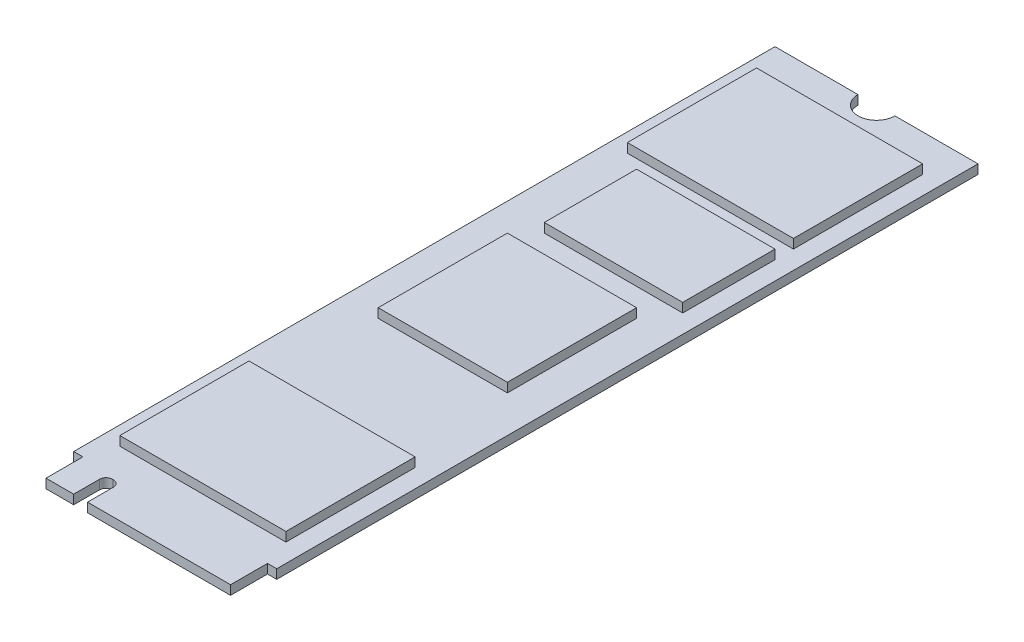
SolidWorks part; units mm, degrees
ref_plane "Front Plane" through (0, 0, 0) normal (0, 0, 1) x (1, 0, 0)
ref_plane "Top Plane" through (0, 0, 0) normal (0, 1, 0) x (1, 0, 0)
ref_plane "Right Plane" through (0, 0, 0) normal (1, 0, 0) x (0, 0, -1)
sketch "Sketch1" plane through (0, 0, 0) normal (0, 1, 0) x (1, 0, 0)
  line L0 (11, 40) -> (-11, 40)
  line L1 (11, 40) -> (11, -36)
  line L2 (11, -36) -> (10, -36)
  line L3 (10, -36) -> (10, -40)
  line L4 (10, -40) -> (-5.5, -40)
  line L5 (-5.5, -40) -> (-5.5, -37.2)
  line L6 (-6.2, -36.5) -> (-6.3, -36.5)
  line L7 (-7, -37.2) -> (-7, -40)
  line L8 (-7, -40) -> (-10, -40)
  line L9 (-10, -40) -> (-10, -36)
  line L10 (-10, -36) -> (-11, -36)
  line L11 (-11, -36) -> (-11, 40)
  arc A0 (-5.5, -37.2) -> (-6.2, -36.5) centre (-6.2, -37.2) ccw
  arc A1 (-6.3, -36.5) -> (-7, -37.2) centre (-6.3, -37.2) ccw
  point P14 (-5.5, -36.5)
  dimension "D13" = 0.7
  dimension "D1" = 22
  dimension "D2" = 80
  dimension "D3" = 80
  dimension "D4" = 76
  dimension "D5" = 76
  dimension "D6" = 40
  dimension "D7" = 11
  dimension "D8" = 20
  dimension "D9" = 10
  dimension "D10" = 3
  dimension "D11" = 15.5
  dimension "D12" = 3.5
extrude "Boss-Extrude1" add sketch "Sketch1" along normal blind 1
sketch "Sketch2" plane through (0, 1, 0) normal (0, 1, 0) x (1, 0, 0)
  line L0 (11, 40) -> (-11, 40) construction
  circle A0 centre (0, 40) radius 2
  dimension "D1" = 4
extrude "Cut-Extrude1" cut sketch "Sketch2" against normal through all
sketch "Sketch4" plane through (0, 1, 0) normal (0, 1, 0) x (1, 0, 0)
  line L0 (-11, 40) -> (-11, -36) construction
  line L1 (-9, 36) -> (9, 36)
  line L2 (-9, 36) -> (-9, 22)
  line L3 (-9, 22) -> (9, 22)
  line L4 (9, 36) -> (9, 22)
  line L5 (-6, 20) -> (9, 20)
  line L6 (-6, 20) -> (-6, 10)
  line L7 (-6, 10) -> (9, 10)
  line L8 (9, 20) -> (9, 10)
  line L9 (-7, 7) -> (7, 7)
  line L10 (-7, 7) -> (-7, -7)
  line L11 (-7, -7) -> (7, -7)
  line L12 (7, 7) -> (7, -7)
  line L13 (-9, -19) -> (9, -19)
  line L14 (-9, -19) -> (-9, -33)
  line L15 (-9, -33) -> (9, -33)
  line L16 (9, -19) -> (9, -33)
  line L17 (-5.5, -40) -> (10, -40) construction
  line L18 (-2, 40) -> (-11, 40) construction
  line L19 (11, -36) -> (11, 40) construction
  dimension "D1" = 18
  dimension "D2" = 14
  dimension "D3" = 2
  dimension "D4" = 7
  dimension "D5" = 18
  dimension "D6" = 14
  dimension "D7" = 2
  dimension "D8" = 4
  dimension "D9" = 15
  dimension "D10" = 10
  dimension "D11" = 2
  dimension "D12" = 2
  dimension "D13" = 14
  dimension "D14" = 14
  dimension "D15" = 4
  dimension "D16" = 3
extrude "Boss-Extrude2" add sketch "Sketch4" along normal blind 1
